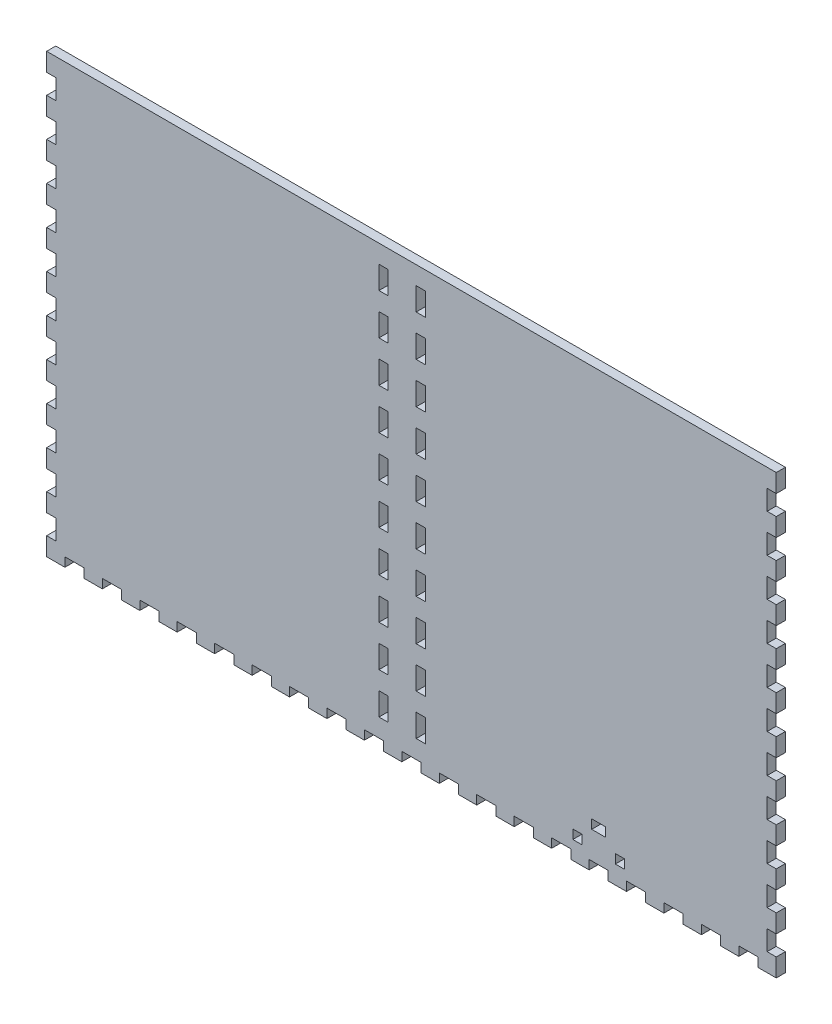
SolidWorks part; units mm, degrees
material "Acrylic (Medium-high impact)"
ref_plane "Front Plane" through (0, 0, 0) normal (0, 0, 1) x (1, 0, 0)
ref_plane "Top Plane" through (0, 0, 0) normal (0, 1, 0) x (1, 0, 0)
ref_plane "Right Plane" through (0, 0, 0) normal (1, 0, 0) x (0, 0, -1)
sketch "Sketch1" plane through (0, 0, 0) normal (0, 1, 0) x (1, 0, 0)
  line L1 (-254, 95.25) -> (254, 95.25)
  line L2 (-254, 95.25) -> (-254, -95.25)
  line L3 (-254, -95.25) -> (254, -95.25)
  line L4 (254, 95.25) -> (254, -95.25)
  point P4 (-254, 0)
  point P6 (0, 95.25)
  dimension "D1" = 190.5
  dimension "D2" = 508
extrude "Boss-Extrude1" add sketch "Sketch1" along normal blind 6.35
sketch "Sketch2" plane through (0, 6.35, 0) normal (0, 1, 0) x (1, 0, 0)
  line L0 (254, -95.25) -> (254, 95.25) construction
  line L1 (-254, 95.25) -> (254, 95.25)
  line L2 (-254, 95.25) -> (-254, -95.25)
  line L3 (-254, -95.25) -> (254, -95.25)
  line L4 (254, 95.25) -> (254, -95.25)
  line L5 (-254, -95.25) -> (254, -95.25) construction
  line L7 (-247.65, 88.9) -> (247.65, 88.9)
  line L8 (-247.65, 88.9) -> (-247.65, -88.9)
  line L9 (-247.65, -88.9) -> (247.65, -88.9)
  line L10 (247.65, 88.9) -> (247.65, -88.9)
  point P7 (-247.65, 0)
  point P14 (-254, 0)
  point P15 (0, -88.9)
  point P16 (0, -95.25)
  point P17 (247.65, 0)
  point P18 (254, 0)
  dimension "D1" = 6.35
  dimension "D2" = 6.35
extrude "Boss-Extrude2" add sketch "Sketch2" along normal blind 298.45
sketch "Sketch3" plane through (0, 0, 95.25) normal (0, 0, 1) x (1, 0, 0)
  line L0 (0, 304.8) -> (0, 0) construction
  line L1 (-254, 304.8) -> (254, 304.8) construction
  line L2 (-247.65, 6.35) -> (247.65, 6.35) construction
  line L4 (-3.302, 283.21) -> (-3.302, 6.35)
  line L5 (-3.302, 6.35) -> (3.302, 6.35)
  line L6 (3.302, 292.354) -> (3.302, 6.35)
  line L7 (3.302, 292.354) -> (-16.256, 292.354)
  line L9 (-5.842, 285.75) -> (-16.256, 285.75)
  line L10 (-16.256, 292.354) -> (-16.256, 285.75)
  line L11 (3.302, 101.6) -> (16.002, 101.6) construction
  line L12 (-254, 0) -> (254, 0) construction
  line L13 (12.827, 88.9) -> (12.827, 101.6) construction
  line L14 (9.652, 88.9) -> (16.002, 88.9)
  line L15 (9.652, 88.9) -> (9.652, 71.9667)
  line L16 (9.652, 71.9667) -> (16.002, 71.9667)
  line L17 (16.002, 88.9) -> (16.002, 71.9667)
  line L18 (9.652, 42.3333) -> (16.002, 42.3333)
  line L19 (9.652, 42.3333) -> (9.652, 59.2667)
  line L20 (9.652, 59.2667) -> (16.002, 59.2667)
  line L21 (16.002, 42.3333) -> (16.002, 59.2667)
  line L26 (9.652, 29.6333) -> (16.002, 29.6333)
  line L27 (9.652, 29.6333) -> (9.652, 12.7)
  line L28 (9.652, 12.7) -> (16.002, 12.7)
  line L29 (16.002, 29.6333) -> (16.002, 12.7)
  line L30 (12.827, 59.2667) -> (12.827, 71.9667) construction
  line L31 (12.827, 29.6333) -> (12.827, 42.3333) construction
  line L32 (12.827, 12.7) -> (12.827, 0) construction
  arc A0 (-3.302, 283.21) -> (-5.842, 285.75) centre (-5.842, 283.21) ccw
  point P5 (0, 6.35)
  dimension "D5" = 2.54
  dimension "D1" = 6.604
  dimension "D2" = 12.954
  dimension "D3" = 6.604
  dimension "D4" = 286.004
  dimension "D6" = 101.6
  dimension "D7" = 12.7
  dimension "D8" = 12.7
  dimension "D9" = 6.35
extrude "Cut-Extrude1" cut sketch "Sketch3" against normal blind 12.7
sketch "Sketch4" plane through (0, 0, -88.9) normal (0, 0, 1) x (1, 0, 0)
  line L0 (-254, 304.8) -> (254, 304.8) construction
  line L1 (-22.606, 304.8) -> (-16.256, 304.8)
  line L2 (-22.606, 304.8) -> (-22.606, 6.35)
  line L3 (-22.606, 6.35) -> (-16.256, 6.35)
  line L4 (-16.256, 304.8) -> (-16.256, 6.35)
  line L5 (6.477, 263.525) -> (6.477, 247.65) construction
  line L6 (-16.256, 292.354) -> (-16.256, 285.75) construction
  line L7 (3.302, 304.8) -> (9.652, 304.8)
  line L8 (3.302, 304.8) -> (3.302, 6.35)
  line L9 (3.302, 6.35) -> (9.652, 6.35)
  line L10 (9.652, 304.8) -> (9.652, 6.35)
  line L11 (247.65, 6.35) -> (-247.65, 6.35) construction
  line L12 (3.302, 6.35) -> (3.302, 292.354) construction
  line L13 (-16.256, 304.8) -> (-22.606, 304.8)
  line L14 (-16.256, 304.8) -> (-16.256, 292.1)
  line L15 (-16.256, 292.1) -> (-22.606, 292.1)
  line L16 (-22.606, 304.8) -> (-22.606, 292.1)
  line L17 (-16.256, 276.225) -> (-22.606, 276.225)
  line L18 (-16.256, 276.225) -> (-16.256, 263.525)
  line L19 (-16.256, 263.525) -> (-22.606, 263.525)
  line L20 (-22.606, 276.225) -> (-22.606, 263.525)
  line L21 (-22.606, 6.35) -> (-16.256, 6.35)
  line L22 (-22.606, 6.35) -> (-22.606, 19.05)
  line L23 (-22.606, 19.05) -> (-16.256, 19.05)
  line L24 (-16.256, 6.35) -> (-16.256, 19.05)
  line L25 (-22.606, 34.925) -> (-16.256, 34.925)
  line L26 (-22.606, 34.925) -> (-22.606, 47.625)
  line L27 (-22.606, 47.625) -> (-16.256, 47.625)
  line L28 (-16.256, 34.925) -> (-16.256, 47.625)
  line L29 (-22.606, 92.075) -> (-16.256, 92.075)
  line L30 (-22.606, 92.075) -> (-22.606, 104.775)
  line L31 (-22.606, 104.775) -> (-16.256, 104.775)
  line L32 (-16.256, 92.075) -> (-16.256, 104.775)
  line L33 (-22.606, 149.225) -> (-16.256, 149.225)
  line L34 (-22.606, 149.225) -> (-22.606, 161.925)
  line L35 (-22.606, 161.925) -> (-16.256, 161.925)
  line L36 (-16.256, 149.225) -> (-16.256, 161.925)
  line L37 (-22.606, 177.8) -> (-16.256, 177.8)
  line L38 (-22.606, 177.8) -> (-22.606, 190.5)
  line L39 (-22.606, 190.5) -> (-16.256, 190.5)
  line L40 (-16.256, 177.8) -> (-16.256, 190.5)
  line L41 (-22.606, 206.375) -> (-16.256, 206.375)
  line L42 (-22.606, 206.375) -> (-22.606, 219.075)
  line L43 (-22.606, 219.075) -> (-16.256, 219.075)
  line L44 (-16.256, 206.375) -> (-16.256, 219.075)
  line L45 (-22.606, 234.95) -> (-16.256, 234.95)
  line L46 (-22.606, 234.95) -> (-22.606, 247.65)
  line L47 (-22.606, 247.65) -> (-16.256, 247.65)
  line L48 (-16.256, 234.95) -> (-16.256, 247.65)
  line L49 (-16.256, 133.35) -> (-22.606, 133.35)
  line L50 (-16.256, 133.35) -> (-16.256, 120.65)
  line L51 (-16.256, 120.65) -> (-22.606, 120.65)
  line L52 (-22.606, 133.35) -> (-22.606, 120.65)
  line L53 (-16.256, 76.2) -> (-22.606, 76.2)
  line L54 (-16.256, 76.2) -> (-16.256, 63.5)
  line L55 (-16.256, 63.5) -> (-22.606, 63.5)
  line L56 (-22.606, 76.2) -> (-22.606, 63.5)
  line L57 (-19.431, 304.8) -> (-19.431, 292.1) construction
  line L58 (-19.431, 292.1) -> (-19.431, 276.225) construction
  line L59 (-19.431, 276.225) -> (-19.431, 263.525) construction
  line L60 (-19.431, 247.65) -> (-19.431, 234.95) construction
  line L61 (-19.431, 234.95) -> (-19.431, 219.075) construction
  line L62 (-19.431, 219.075) -> (-19.431, 206.375) construction
  line L63 (-19.431, 206.375) -> (-19.431, 190.5) construction
  line L64 (-19.431, 190.5) -> (-19.431, 177.8) construction
  line L65 (-19.431, 177.8) -> (-19.431, 161.925) construction
  line L66 (-19.431, 161.925) -> (-19.431, 149.225) construction
  line L67 (-19.431, 133.35) -> (-19.431, 120.65) construction
  line L68 (-19.431, 120.65) -> (-19.431, 104.775) construction
  line L69 (-19.431, 104.775) -> (-19.431, 92.075) construction
  line L70 (-19.431, 92.075) -> (-19.431, 76.2) construction
  line L71 (-19.431, 76.2) -> (-19.431, 63.5) construction
  line L72 (-19.431, 63.5) -> (-19.431, 47.625) construction
  line L73 (-19.431, 47.625) -> (-19.431, 34.925) construction
  line L74 (-19.431, 34.925) -> (-19.431, 19.05) construction
  line L75 (-19.431, 19.05) -> (-19.431, 6.35) construction
  line L76 (-19.431, 149.225) -> (-19.431, 133.35) construction
  line L77 (-19.431, 263.525) -> (-19.431, 247.65) construction
  line L78 (-6.477, 304.8) -> (-6.477, 0) construction
  line L79 (254, 304.8) -> (-254, 304.8) construction
  line L80 (254, 0) -> (-254, 0) construction
  line L81 (-6.477, 8.3493) -> (3.302, 8.3493) construction
  line L82 (-6.477, 8.3493) -> (-16.256, 8.3493) construction
  line L83 (6.477, 149.225) -> (6.477, 133.35) construction
  line L84 (6.477, 19.05) -> (6.477, 6.35) construction
  line L85 (6.477, 34.925) -> (6.477, 19.05) construction
  line L86 (6.477, 47.625) -> (6.477, 34.925) construction
  line L87 (6.477, 63.5) -> (6.477, 47.625) construction
  line L88 (6.477, 76.2) -> (6.477, 63.5) construction
  line L89 (6.477, 92.075) -> (6.477, 76.2) construction
  line L90 (6.477, 104.775) -> (6.477, 92.075) construction
  line L91 (6.477, 120.65) -> (6.477, 104.775) construction
  line L92 (6.477, 133.35) -> (6.477, 120.65) construction
  line L93 (6.477, 161.925) -> (6.477, 149.225) construction
  line L94 (6.477, 177.8) -> (6.477, 161.925) construction
  line L95 (6.477, 190.5) -> (6.477, 177.8) construction
  line L96 (6.477, 206.375) -> (6.477, 190.5) construction
  line L97 (6.477, 219.075) -> (6.477, 206.375) construction
  line L98 (6.477, 234.95) -> (6.477, 219.075) construction
  line L99 (6.477, 247.65) -> (6.477, 234.95) construction
  line L100 (6.477, 276.225) -> (6.477, 263.525) construction
  line L101 (6.477, 292.1) -> (6.477, 276.225) construction
  line L102 (6.477, 304.8) -> (6.477, 292.1) construction
  line L103 (9.652, 76.2) -> (9.652, 63.5)
  line L104 (3.302, 63.5) -> (9.652, 63.5)
  line L105 (3.302, 76.2) -> (3.302, 63.5)
  line L106 (3.302, 76.2) -> (9.652, 76.2)
  line L107 (9.652, 133.35) -> (9.652, 120.65)
  line L108 (3.302, 120.65) -> (9.652, 120.65)
  line L109 (3.302, 133.35) -> (3.302, 120.65)
  line L110 (3.302, 133.35) -> (9.652, 133.35)
  line L111 (3.302, 234.95) -> (3.302, 247.65)
  line L112 (9.652, 247.65) -> (3.302, 247.65)
  line L113 (9.652, 234.95) -> (9.652, 247.65)
  line L114 (9.652, 234.95) -> (3.302, 234.95)
  line L115 (3.302, 206.375) -> (3.302, 219.075)
  line L116 (9.652, 219.075) -> (3.302, 219.075)
  line L117 (9.652, 206.375) -> (9.652, 219.075)
  line L118 (9.652, 206.375) -> (3.302, 206.375)
  line L119 (3.302, 177.8) -> (3.302, 190.5)
  line L120 (9.652, 190.5) -> (3.302, 190.5)
  line L121 (9.652, 177.8) -> (9.652, 190.5)
  line L122 (9.652, 177.8) -> (3.302, 177.8)
  line L123 (3.302, 149.225) -> (3.302, 161.925)
  line L124 (9.652, 161.925) -> (3.302, 161.925)
  line L125 (9.652, 149.225) -> (9.652, 161.925)
  line L126 (9.652, 149.225) -> (3.302, 149.225)
  line L127 (3.302, 92.075) -> (3.302, 104.775)
  line L128 (9.652, 104.775) -> (3.302, 104.775)
  line L129 (9.652, 92.075) -> (9.652, 104.775)
  line L130 (9.652, 92.075) -> (3.302, 92.075)
  line L131 (3.302, 34.925) -> (3.302, 47.625)
  line L132 (9.652, 47.625) -> (3.302, 47.625)
  line L133 (9.652, 34.925) -> (9.652, 47.625)
  line L134 (9.652, 34.925) -> (3.302, 34.925)
  line L135 (3.302, 6.35) -> (3.302, 19.05)
  line L136 (9.652, 19.05) -> (3.302, 19.05)
  line L137 (9.652, 6.35) -> (9.652, 19.05)
  line L138 (9.652, 6.35) -> (3.302, 6.35)
  line L139 (9.652, 276.225) -> (9.652, 263.525)
  line L140 (3.302, 263.525) -> (9.652, 263.525)
  line L141 (3.302, 276.225) -> (3.302, 263.525)
  line L142 (3.302, 276.225) -> (9.652, 276.225)
  line L143 (9.652, 304.8) -> (9.652, 292.1)
  line L144 (3.302, 292.1) -> (9.652, 292.1)
  line L145 (3.302, 304.8) -> (3.302, 292.1)
  line L146 (3.302, 304.8) -> (9.652, 304.8)
  line L147 (3.302, 304.8) -> (3.302, 6.35)
  line L148 (9.652, 6.35) -> (3.302, 6.35)
  line L149 (9.652, 304.8) -> (9.652, 6.35)
  line L150 (9.652, 304.8) -> (3.302, 304.8)
  point P14 (-16.256, 289.052)
  dimension "D1" = 6.35
  dimension "D2" = 12.7
extrude "Cut-Extrude2" cut sketch "Sketch4" against normal up to next (6.35 mm away) contours L17 L4 L15 L2 | L2 L47 L4 L19 | L45 L2 L43 L4 | L41 L2 L39 L4 | L37 L2 L35 L4 | L49 L4 L33 L2 | L4 L51 L2 L31 | L53 L4 L29 L2 | L4 L55 L2 L27 | L25 L2 L23 L4
ref_plane "Plane1" through (-6.477, 0, 0) normal (-1, 0, 0) x (0, 0, 1)
mirror "Mirror1" about plane through (-6.477, 0, 0) normal (-1, 0, 0) of "Cut-Extrude2"
sketch "Sketch5" plane through (0, 0, 0) normal (0, -1, 0) x (-1, 0, 0)
  line L0 (-227.9316, -95.25) -> (-227.9316, -88.9)
  line L1 (-247.65, 88.9) -> (247.65, 88.9)
  line L2 (-247.65, 88.9) -> (-247.65, -88.9)
  line L3 (-247.65, -88.9) -> (247.65, -88.9)
  line L4 (247.65, 88.9) -> (247.65, -88.9)
  line L5 (-254, -95.25) -> (-241.3, -95.25)
  line L6 (-254, -95.25) -> (-254, -88.9)
  line L7 (-254, -88.9) -> (-241.3, -88.9)
  line L8 (-241.3, -95.25) -> (-241.3, -88.9)
  line L9 (-227.9316, -95.25) -> (-215.2316, -95.25)
  line L10 (-227.9316, -88.9) -> (-215.2316, -88.9)
  line L11 (-215.2316, -95.25) -> (-215.2316, -88.9)
  line L12 (-201.8632, -95.25) -> (-201.8632, -88.9)
  line L13 (-201.8632, -95.25) -> (-189.1632, -95.25)
  line L14 (-201.8632, -88.9) -> (-189.1632, -88.9)
  line L15 (-189.1632, -95.25) -> (-189.1632, -88.9)
  line L16 (-175.7947, -95.25) -> (-175.7947, -88.9)
  line L17 (-175.7947, -95.25) -> (-163.0947, -95.25)
  line L18 (-175.7947, -88.9) -> (-163.0947, -88.9)
  line L19 (-163.0947, -95.25) -> (-163.0947, -88.9)
  line L20 (-149.7263, -95.25) -> (-149.7263, -88.9)
  line L21 (-149.7263, -95.25) -> (-137.0263, -95.25)
  line L22 (-149.7263, -88.9) -> (-137.0263, -88.9)
  line L23 (-137.0263, -95.25) -> (-137.0263, -88.9)
  line L24 (-123.6579, -95.25) -> (-123.6579, -88.9)
  line L25 (-123.6579, -95.25) -> (-110.9579, -95.25)
  line L26 (-123.6579, -88.9) -> (-110.9579, -88.9)
  line L27 (-110.9579, -95.25) -> (-110.9579, -88.9)
  line L28 (-97.5895, -95.25) -> (-97.5895, -88.9)
  line L29 (-97.5895, -95.25) -> (-84.8895, -95.25)
  line L30 (-97.5895, -88.9) -> (-84.8895, -88.9)
  line L31 (-84.8895, -95.25) -> (-84.8895, -88.9)
  line L32 (-71.5211, -95.25) -> (-71.5211, -88.9)
  line L33 (-71.5211, -95.25) -> (-58.8211, -95.25)
  line L34 (-71.5211, -88.9) -> (-58.8211, -88.9)
  line L35 (-58.8211, -95.25) -> (-58.8211, -88.9)
  line L36 (-45.4526, -95.25) -> (-45.4526, -88.9)
  line L37 (-45.4526, -95.25) -> (-32.7526, -95.25)
  line L38 (-45.4526, -88.9) -> (-32.7526, -88.9)
  line L39 (-32.7526, -95.25) -> (-32.7526, -88.9)
  line L40 (-19.3842, -95.25) -> (-19.3842, -88.9)
  line L41 (-19.3842, -95.25) -> (-6.6842, -95.25)
  line L42 (-19.3842, -88.9) -> (-6.6842, -88.9)
  line L43 (-6.6842, -95.25) -> (-6.6842, -88.9)
  line L44 (6.6842, -95.25) -> (6.6842, -88.9)
  line L45 (6.6842, -95.25) -> (19.3842, -95.25)
  line L46 (6.6842, -88.9) -> (19.3842, -88.9)
  line L47 (19.3842, -95.25) -> (19.3842, -88.9)
  line L48 (32.7526, -95.25) -> (32.7526, -88.9)
  line L49 (32.7526, -95.25) -> (45.4526, -95.25)
  line L50 (32.7526, -88.9) -> (45.4526, -88.9)
  line L51 (45.4526, -95.25) -> (45.4526, -88.9)
  line L52 (58.8211, -95.25) -> (58.8211, -88.9)
  line L53 (58.8211, -95.25) -> (71.5211, -95.25)
  line L54 (58.8211, -88.9) -> (71.5211, -88.9)
  line L55 (71.5211, -95.25) -> (71.5211, -88.9)
  line L56 (84.8895, -95.25) -> (84.8895, -88.9)
  line L57 (84.8895, -95.25) -> (97.5895, -95.25)
  line L58 (84.8895, -88.9) -> (97.5895, -88.9)
  line L59 (97.5895, -95.25) -> (97.5895, -88.9)
  line L60 (110.9579, -95.25) -> (110.9579, -88.9)
  line L61 (110.9579, -95.25) -> (123.6579, -95.25)
  line L62 (110.9579, -88.9) -> (123.6579, -88.9)
  line L63 (123.6579, -95.25) -> (123.6579, -88.9)
  line L64 (137.0263, -95.25) -> (137.0263, -88.9)
  line L65 (137.0263, -95.25) -> (149.7263, -95.25)
  line L66 (137.0263, -88.9) -> (149.7263, -88.9)
  line L67 (149.7263, -95.25) -> (149.7263, -88.9)
  line L68 (163.0947, -95.25) -> (163.0947, -88.9)
  line L69 (163.0947, -95.25) -> (175.7947, -95.25)
  line L70 (163.0947, -88.9) -> (175.7947, -88.9)
  line L71 (175.7947, -95.25) -> (175.7947, -88.9)
  line L72 (189.1632, -95.25) -> (189.1632, -88.9)
  line L73 (189.1632, -95.25) -> (201.8632, -95.25)
  line L74 (189.1632, -88.9) -> (201.8632, -88.9)
  line L75 (201.8632, -95.25) -> (201.8632, -88.9)
  line L76 (215.2316, -95.25) -> (215.2316, -88.9)
  line L77 (215.2316, -95.25) -> (227.9316, -95.25)
  line L78 (215.2316, -88.9) -> (227.9316, -88.9)
  line L79 (227.9316, -95.25) -> (227.9316, -88.9)
  line L80 (241.3, -95.25) -> (241.3, -88.9)
  line L81 (241.3, -95.25) -> (254, -95.25)
  line L82 (241.3, -88.9) -> (254, -88.9)
  line L83 (254, -95.25) -> (254, -88.9)
  line L84 (-167.64, 0) -> (167.64, 0) construction
  line L85 (254, 95.25) -> (254, 88.9)
  line L86 (241.3, 88.9) -> (254, 88.9)
  line L87 (241.3, 95.25) -> (254, 95.25)
  line L88 (241.3, 95.25) -> (241.3, 88.9)
  line L89 (227.9316, 95.25) -> (227.9316, 88.9)
  line L90 (215.2316, 88.9) -> (227.9316, 88.9)
  line L91 (215.2316, 95.25) -> (227.9316, 95.25)
  line L92 (215.2316, 95.25) -> (215.2316, 88.9)
  line L93 (201.8632, 95.25) -> (201.8632, 88.9)
  line L94 (189.1632, 88.9) -> (201.8632, 88.9)
  line L95 (189.1632, 95.25) -> (201.8632, 95.25)
  line L96 (189.1632, 95.25) -> (189.1632, 88.9)
  line L97 (175.7947, 95.25) -> (175.7947, 88.9)
  line L98 (163.0947, 88.9) -> (175.7947, 88.9)
  line L99 (163.0947, 95.25) -> (175.7947, 95.25)
  line L100 (163.0947, 95.25) -> (163.0947, 88.9)
  line L101 (149.7263, 95.25) -> (149.7263, 88.9)
  line L102 (137.0263, 88.9) -> (149.7263, 88.9)
  line L103 (137.0263, 95.25) -> (149.7263, 95.25)
  line L104 (137.0263, 95.25) -> (137.0263, 88.9)
  line L105 (123.6579, 95.25) -> (123.6579, 88.9)
  line L106 (110.9579, 88.9) -> (123.6579, 88.9)
  line L107 (110.9579, 95.25) -> (123.6579, 95.25)
  line L108 (110.9579, 95.25) -> (110.9579, 88.9)
  line L109 (97.5895, 95.25) -> (97.5895, 88.9)
  line L110 (84.8895, 88.9) -> (97.5895, 88.9)
  line L111 (84.8895, 95.25) -> (97.5895, 95.25)
  line L112 (84.8895, 95.25) -> (84.8895, 88.9)
  line L113 (71.5211, 95.25) -> (71.5211, 88.9)
  line L114 (58.8211, 88.9) -> (71.5211, 88.9)
  line L115 (58.8211, 95.25) -> (71.5211, 95.25)
  line L116 (58.8211, 95.25) -> (58.8211, 88.9)
  line L117 (45.4526, 95.25) -> (45.4526, 88.9)
  line L118 (32.7526, 88.9) -> (45.4526, 88.9)
  line L119 (32.7526, 95.25) -> (45.4526, 95.25)
  line L120 (32.7526, 95.25) -> (32.7526, 88.9)
  line L121 (19.3842, 95.25) -> (19.3842, 88.9)
  line L122 (6.6842, 88.9) -> (19.3842, 88.9)
  line L123 (6.6842, 95.25) -> (19.3842, 95.25)
  line L124 (6.6842, 95.25) -> (6.6842, 88.9)
  line L125 (-6.6842, 95.25) -> (-6.6842, 88.9)
  line L126 (-19.3842, 88.9) -> (-6.6842, 88.9)
  line L127 (-19.3842, 95.25) -> (-6.6842, 95.25)
  line L128 (-19.3842, 95.25) -> (-19.3842, 88.9)
  line L129 (-32.7526, 95.25) -> (-32.7526, 88.9)
  line L130 (-45.4526, 88.9) -> (-32.7526, 88.9)
  line L131 (-45.4526, 95.25) -> (-32.7526, 95.25)
  line L132 (-45.4526, 95.25) -> (-45.4526, 88.9)
  line L133 (-58.8211, 95.25) -> (-58.8211, 88.9)
  line L134 (-71.5211, 88.9) -> (-58.8211, 88.9)
  line L135 (-71.5211, 95.25) -> (-58.8211, 95.25)
  line L136 (-71.5211, 95.25) -> (-71.5211, 88.9)
  line L137 (-84.8895, 95.25) -> (-84.8895, 88.9)
  line L138 (-97.5895, 88.9) -> (-84.8895, 88.9)
  line L139 (-97.5895, 95.25) -> (-84.8895, 95.25)
  line L140 (-97.5895, 95.25) -> (-97.5895, 88.9)
  line L141 (-110.9579, 95.25) -> (-110.9579, 88.9)
  line L142 (-123.6579, 88.9) -> (-110.9579, 88.9)
  line L143 (-123.6579, 95.25) -> (-110.9579, 95.25)
  line L144 (-123.6579, 95.25) -> (-123.6579, 88.9)
  line L145 (-137.0263, 95.25) -> (-137.0263, 88.9)
  line L146 (-149.7263, 88.9) -> (-137.0263, 88.9)
  line L147 (-149.7263, 95.25) -> (-137.0263, 95.25)
  line L148 (-149.7263, 95.25) -> (-149.7263, 88.9)
  line L149 (-163.0947, 95.25) -> (-163.0947, 88.9)
  line L150 (-175.7947, 88.9) -> (-163.0947, 88.9)
  line L151 (-175.7947, 95.25) -> (-163.0947, 95.25)
  line L152 (-175.7947, 95.25) -> (-175.7947, 88.9)
  line L153 (-189.1632, 95.25) -> (-189.1632, 88.9)
  line L154 (-201.8632, 88.9) -> (-189.1632, 88.9)
  line L155 (-201.8632, 95.25) -> (-189.1632, 95.25)
  line L156 (-201.8632, 95.25) -> (-201.8632, 88.9)
  line L157 (-215.2316, 95.25) -> (-215.2316, 88.9)
  line L158 (-227.9316, 88.9) -> (-215.2316, 88.9)
  line L159 (-227.9316, 95.25) -> (-215.2316, 95.25)
  line L160 (-241.3, 95.25) -> (-241.3, 88.9)
  line L161 (-254, 88.9) -> (-241.3, 88.9)
  line L162 (-254, 95.25) -> (-254, 88.9)
  line L163 (-254, 95.25) -> (-241.3, 95.25)
  line L164 (-247.65, 88.9) -> (247.65, 88.9)
  line L165 (-227.9316, 95.25) -> (-227.9316, 88.9)
  line L166 (-254, 65.6167) -> (-254, 52.9167)
  line L167 (-254, 95.25) -> (-247.65, 95.25)
  line L168 (-254, 95.25) -> (-254, 82.55)
  line L169 (-254, 82.55) -> (-247.65, 82.55)
  line L170 (-247.65, 95.25) -> (-247.65, 82.55)
  line L171 (-254, 65.6167) -> (-247.65, 65.6167)
  line L172 (-247.65, 65.6167) -> (-247.65, 52.9167)
  line L173 (-254, 52.9167) -> (-247.65, 52.9167)
  line L174 (-254, 35.9833) -> (-254, 23.2833)
  line L175 (-254, 35.9833) -> (-247.65, 35.9833)
  line L176 (-247.65, 35.9833) -> (-247.65, 23.2833)
  line L177 (-254, 23.2833) -> (-247.65, 23.2833)
  line L178 (-254, 6.35) -> (-254, -6.35)
  line L179 (-254, 6.35) -> (-247.65, 6.35)
  line L180 (-247.65, 6.35) -> (-247.65, -6.35)
  line L181 (-254, -6.35) -> (-247.65, -6.35)
  line L182 (-254, -23.2833) -> (-254, -35.9833)
  line L183 (-254, -23.2833) -> (-247.65, -23.2833)
  line L184 (-247.65, -23.2833) -> (-247.65, -35.9833)
  line L185 (-254, -35.9833) -> (-247.65, -35.9833)
  line L186 (-254, -52.9167) -> (-254, -65.6167)
  line L187 (-254, -52.9167) -> (-247.65, -52.9167)
  line L188 (-247.65, -52.9167) -> (-247.65, -65.6167)
  line L189 (-254, -65.6167) -> (-247.65, -65.6167)
  line L190 (-254, -82.55) -> (-254, -95.25)
  line L191 (-254, -82.55) -> (-247.65, -82.55)
  line L192 (-247.65, -82.55) -> (-247.65, -95.25)
  line L193 (-254, -95.25) -> (-247.65, -95.25)
  line L194 (0, 104.775) -> (0, -104.775) construction
  line L195 (254, -95.25) -> (247.65, -95.25)
  line L196 (247.65, -82.55) -> (247.65, -95.25)
  line L197 (254, -82.55) -> (247.65, -82.55)
  line L198 (254, -82.55) -> (254, -95.25)
  line L199 (254, -65.6167) -> (247.65, -65.6167)
  line L200 (247.65, -52.9167) -> (247.65, -65.6167)
  line L201 (254, -52.9167) -> (247.65, -52.9167)
  line L202 (254, -52.9167) -> (254, -65.6167)
  line L203 (254, -35.9833) -> (247.65, -35.9833)
  line L204 (247.65, -23.2833) -> (247.65, -35.9833)
  line L205 (254, -23.2833) -> (247.65, -23.2833)
  line L206 (254, -23.2833) -> (254, -35.9833)
  line L207 (254, -6.35) -> (247.65, -6.35)
  line L208 (247.65, 6.35) -> (247.65, -6.35)
  line L209 (254, 6.35) -> (247.65, 6.35)
  line L210 (254, 6.35) -> (254, -6.35)
  line L211 (254, 23.2833) -> (247.65, 23.2833)
  line L212 (247.65, 35.9833) -> (247.65, 23.2833)
  line L213 (254, 35.9833) -> (247.65, 35.9833)
  line L214 (254, 35.9833) -> (254, 23.2833)
  line L215 (254, 52.9167) -> (247.65, 52.9167)
  line L216 (247.65, 65.6167) -> (247.65, 52.9167)
  line L217 (254, 65.6167) -> (247.65, 65.6167)
  line L218 (247.65, 95.25) -> (247.65, 82.55)
  line L219 (254, 82.55) -> (247.65, 82.55)
  line L220 (254, 95.25) -> (254, 82.55)
  line L221 (254, 95.25) -> (247.65, 95.25)
  line L222 (254, 65.6167) -> (254, 52.9167)
  line L223 (254, 95.25) -> (254, 88.9)
  line L224 (254, -95.25) -> (254, -88.9)
  line L225 (247.65, 88.9) -> (247.65, -88.9)
  line M115 (254, 95.25) -> (-254, 95.25)
  dimension "D1" = 12.7
  dimension "D3" = 6.35
  dimension "D5" = 12.7
  dimension "D2" = 20
  dimension "D4" = 7
sketch "Sketch6" plane through (0, 0, 0) normal (0, 1, 0) x (1, 0, 0)
  line L0 (247.65, 88.9) -> (-247.65, 88.9) construction
  line L1 (-260.4023, 88.9) -> (277.6082, 88.9)
  line L2 (-260.4023, 88.9) -> (-260.4023, -96.6128)
  line L3 (-260.4023, -96.6128) -> (277.6082, -96.6128)
  line L4 (277.6082, 88.9) -> (277.6082, -96.6128)
extrude "Cut-Extrude5" cut sketch "Sketch6" along normal through all
extrude "Cut-Extrude6" cut sketch "Sketch5" against normal blind 6.35 contours L165 L160 L1 M115 | L157 L1 L156 M115 | L153 L1 L152 M115 | L149 L1 L148 M115 | L145 L1 L144 M115 | L141 L1 L140 M115 | L137 L1 L136 M115 | L133 L1 L132 M115 | L129 L1 L128 M115 | L125 L1 L124 M115 | L121 L1 L120 M115 | L117 L1 L116 M115 | L113 L1 L112 M115 | L109 L1 L108 M115 | L105 L1 L104 M115 | L101 L1 L100 M115 | L97 L1 L96 M115 | L93 L1 L92 M115 | L89 L1 L88 M115
sketch "Sketch7" plane through (-254, 0, 0) normal (-1, 0, 0) x (0, 0, 1)
  line L0 (-95.25, 26.5545) -> (-95.25, 39.2545)
  line L1 (-95.25, 0) -> (-88.9, 0)
  line L2 (-95.25, 0) -> (-95.25, 12.7)
  line L3 (-95.25, 12.7) -> (-88.9, 12.7)
  line L4 (-88.9, 0) -> (-88.9, 12.7)
  line L5 (-95.25, 39.2545) -> (-88.9, 39.2545)
  line L6 (-88.9, 26.5545) -> (-88.9, 39.2545)
  line L7 (-95.25, 26.5545) -> (-88.9, 26.5545)
  line L8 (-95.25, 53.1091) -> (-95.25, 65.8091)
  line L9 (-95.25, 65.8091) -> (-88.9, 65.8091)
  line L10 (-88.9, 53.1091) -> (-88.9, 65.8091)
  line L11 (-95.25, 53.1091) -> (-88.9, 53.1091)
  line L12 (-95.25, 79.6636) -> (-95.25, 92.3636)
  line L13 (-95.25, 92.3636) -> (-88.9, 92.3636)
  line L14 (-88.9, 79.6636) -> (-88.9, 92.3636)
  line L15 (-95.25, 79.6636) -> (-88.9, 79.6636)
  line L16 (-95.25, 106.2182) -> (-95.25, 118.9182)
  line L17 (-95.25, 118.9182) -> (-88.9, 118.9182)
  line L18 (-88.9, 106.2182) -> (-88.9, 118.9182)
  line L19 (-95.25, 106.2182) -> (-88.9, 106.2182)
  line L20 (-95.25, 132.7727) -> (-95.25, 145.4727)
  line L21 (-95.25, 145.4727) -> (-88.9, 145.4727)
  line L22 (-88.9, 132.7727) -> (-88.9, 145.4727)
  line L23 (-95.25, 132.7727) -> (-88.9, 132.7727)
  line L24 (-95.25, 159.3273) -> (-95.25, 172.0273)
  line L25 (-95.25, 172.0273) -> (-88.9, 172.0273)
  line L26 (-88.9, 159.3273) -> (-88.9, 172.0273)
  line L27 (-95.25, 159.3273) -> (-88.9, 159.3273)
  line L28 (-95.25, 185.8818) -> (-95.25, 198.5818)
  line L29 (-95.25, 198.5818) -> (-88.9, 198.5818)
  line L30 (-88.9, 185.8818) -> (-88.9, 198.5818)
  line L31 (-95.25, 185.8818) -> (-88.9, 185.8818)
  line L32 (-95.25, 212.4364) -> (-95.25, 225.1364)
  line L33 (-95.25, 225.1364) -> (-88.9, 225.1364)
  line L34 (-88.9, 212.4364) -> (-88.9, 225.1364)
  line L35 (-95.25, 212.4364) -> (-88.9, 212.4364)
  line L36 (-95.25, 238.9909) -> (-95.25, 251.6909)
  line L37 (-95.25, 251.6909) -> (-88.9, 251.6909)
  line L38 (-88.9, 238.9909) -> (-88.9, 251.6909)
  line L39 (-95.25, 238.9909) -> (-88.9, 238.9909)
  line L40 (-95.25, 265.5455) -> (-95.25, 278.2455)
  line L41 (-95.25, 278.2455) -> (-88.9, 278.2455)
  line L42 (-88.9, 265.5455) -> (-88.9, 278.2455)
  line L43 (-95.25, 265.5455) -> (-88.9, 265.5455)
  line L44 (-95.25, 292.1) -> (-95.25, 304.8)
  line L45 (-95.25, 304.8) -> (-88.9, 304.8)
  line L46 (-88.9, 292.1) -> (-88.9, 304.8)
  line L47 (-95.25, 292.1) -> (-88.9, 292.1)
  line L48 (0, -167.64) -> (0, 167.64) construction
  line L49 (95.25, 292.1) -> (88.9, 292.1)
  line L50 (88.9, 292.1) -> (88.9, 304.8)
  line L51 (95.25, 304.8) -> (88.9, 304.8)
  line L52 (95.25, 292.1) -> (95.25, 304.8)
  line L53 (95.25, 265.5455) -> (88.9, 265.5455)
  line L54 (88.9, 265.5455) -> (88.9, 278.2455)
  line L55 (95.25, 278.2455) -> (88.9, 278.2455)
  line L56 (95.25, 265.5455) -> (95.25, 278.2455)
  line L57 (95.25, 238.9909) -> (88.9, 238.9909)
  line L58 (88.9, 238.9909) -> (88.9, 251.6909)
  line L59 (95.25, 251.6909) -> (88.9, 251.6909)
  line L60 (95.25, 238.9909) -> (95.25, 251.6909)
  line L61 (95.25, 212.4364) -> (88.9, 212.4364)
  line L62 (88.9, 212.4364) -> (88.9, 225.1364)
  line L63 (95.25, 225.1364) -> (88.9, 225.1364)
  line L64 (95.25, 212.4364) -> (95.25, 225.1364)
  line L65 (95.25, 185.8818) -> (88.9, 185.8818)
  line L66 (88.9, 185.8818) -> (88.9, 198.5818)
  line L67 (95.25, 198.5818) -> (88.9, 198.5818)
  line L68 (95.25, 185.8818) -> (95.25, 198.5818)
  line L69 (95.25, 159.3273) -> (88.9, 159.3273)
  line L70 (88.9, 159.3273) -> (88.9, 172.0273)
  line L71 (95.25, 172.0273) -> (88.9, 172.0273)
  line L72 (95.25, 159.3273) -> (95.25, 172.0273)
  line L73 (95.25, 132.7727) -> (88.9, 132.7727)
  line L74 (88.9, 132.7727) -> (88.9, 145.4727)
  line L75 (95.25, 145.4727) -> (88.9, 145.4727)
  line L76 (95.25, 132.7727) -> (95.25, 145.4727)
  line L77 (95.25, 106.2182) -> (88.9, 106.2182)
  line L78 (88.9, 106.2182) -> (88.9, 118.9182)
  line L79 (95.25, 118.9182) -> (88.9, 118.9182)
  line L80 (95.25, 106.2182) -> (95.25, 118.9182)
  line L81 (95.25, 79.6636) -> (88.9, 79.6636)
  line L82 (88.9, 79.6636) -> (88.9, 92.3636)
  line L83 (95.25, 92.3636) -> (88.9, 92.3636)
  line L84 (95.25, 79.6636) -> (95.25, 92.3636)
  line L85 (95.25, 53.1091) -> (88.9, 53.1091)
  line L86 (88.9, 53.1091) -> (88.9, 65.8091)
  line L87 (95.25, 65.8091) -> (88.9, 65.8091)
  line L88 (95.25, 53.1091) -> (95.25, 65.8091)
  line L89 (95.25, 26.5545) -> (88.9, 26.5545)
  line L90 (88.9, 26.5545) -> (88.9, 39.2545)
  line L91 (95.25, 39.2545) -> (88.9, 39.2545)
  line L92 (88.9, 0) -> (88.9, 12.7)
  line L93 (95.25, 12.7) -> (88.9, 12.7)
  line L94 (95.25, 0) -> (95.25, 12.7)
  line L95 (95.25, 0) -> (88.9, 0)
  line L96 (95.25, 26.5545) -> (95.25, 39.2545)
  line L98 (95.25, 304.8) -> (88.9, 304.8)
  line L99 (95.25, 304.8) -> (95.25, 0)
  line L100 (95.25, 0) -> (88.9, 0)
  line L101 (88.9, 304.8) -> (88.9, 0)
  line M52 (-95.25, 304.8) -> (-95.25, 0)
  line M53 (-88.9, 0) -> (-88.9, 304.8)
  dimension "D1" = 12.7
  dimension "D2" = 6.35
  dimension "D3" = 12
extrude "Cut-Extrude8" cut sketch "Sketch7" against normal blind 6.35 contours L47 L41 M52 M53 | L43 L37 M52 M53 | L39 L33 M52 M53 | L35 L29 M52 M53 | L31 L25 M52 M53 | L27 L21 M52 M53 | L23 L17 M52 M53 | L19 L13 M52 M53 | L15 L9 M52 M53 | L11 L5 M52 M53 | L7 L3 M52 M53
mirror "Mirror2" about plane through (0, 0, 0) normal (1, 0, 0) of "Cut-Extrude8"
sketch "Sketch8" plane through (0, 0, -95.25) normal (0, 0, -1) x (-1, 0, 0)
  line L0 (110.9579, 0) -> (123.6579, 0) construction
  line L1 (-135.1681, 31.75) -> (-125.5161, 31.75)
  line L2 (-135.1681, 31.75) -> (-135.1681, 25.4)
  line L3 (-135.1681, 25.4) -> (-125.5161, 25.4)
  line L4 (-125.5161, 31.75) -> (-125.5161, 25.4)
  line L7 (-123.6579, 6.35) -> (-137.0263, 6.35) construction
  line L8 (-149.7263, 0) -> (-137.0263, 0) construction
  line L9 (-148.3126, 19.05) -> (-141.9626, 19.05)
  line L10 (-148.3126, 19.05) -> (-148.3126, 12.7)
  line L11 (-148.3126, 12.7) -> (-141.9626, 12.7)
  line L12 (-141.9626, 19.05) -> (-141.9626, 12.7)
  line L13 (-118.7216, 19.05) -> (-112.3716, 19.05)
  line L14 (-118.7216, 19.05) -> (-118.7216, 12.7)
  line L15 (-118.7216, 12.7) -> (-112.3716, 12.7)
  line L16 (-112.3716, 19.05) -> (-112.3716, 12.7)
  line L17 (-141.9626, 15.875) -> (-118.7216, 15.875) construction
  point P6 (-130.3421, 25.4)
  point P9 (-130.3421, 6.35)
  point P18 (-145.1376, 12.7)
  point P21 (-130.3421, 15.875)
  dimension "D1" = 9.652
  dimension "D2" = 6.35
  dimension "D3" = 25.4
  dimension "D4" = 6.35
  dimension "D5" = 6.35
  dimension "D6" = 12.7
  dimension "D7" = 23.241
extrude "Lever Hole" cut sketch "Sketch8" against normal through all
